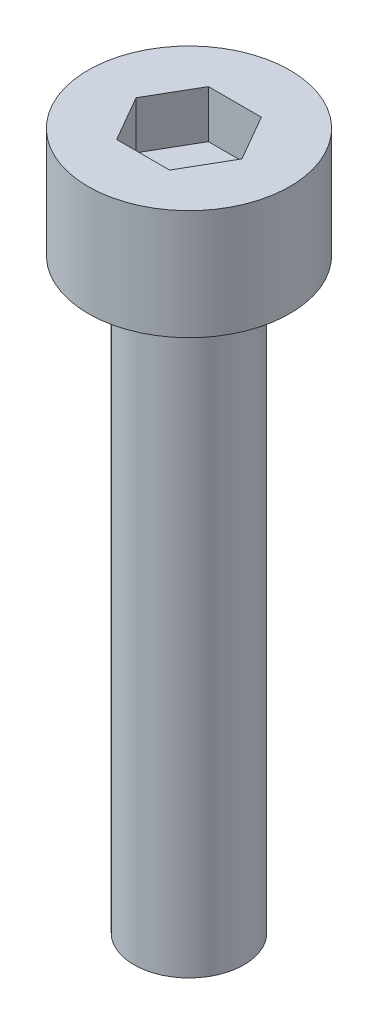
SolidWorks part; units mm, degrees
material "AISI 304"
ref_plane "前视基准面" through (0, 0, 0) normal (0, 0, 1) x (1, 0, 0)
ref_plane "上视基准面" through (0, 0, 0) normal (0, 1, 0) x (1, 0, 0)
ref_plane "右视基准面" through (0, 0, 0) normal (1, 0, 0) x (0, 0, -1)
sketch "草图1" plane through (0, 0, 0) normal (0, 1, 0) x (1, 0, 0)
  circle A0 centre (0, 0) radius 2.75
  dimension "D1" = 5.5
extrude "杯头" add sketch "草图1" along normal blind 3
sketch "草图2" plane through (0, 3, 0) normal (0, 1, 0) x (1, 0, 0)
  line L1 (1.4434, 0) -> (0.7217, 1.25)
  line L2 (0.7217, 1.25) -> (-0.7217, 1.25)
  line L3 (-0.7217, 1.25) -> (-1.4434, 0)
  line L4 (-1.4434, 0) -> (-0.7217, -1.25)
  line L5 (-0.7217, -1.25) -> (0.7217, -1.25)
  line L6 (0.7217, -1.25) -> (1.4434, 0)
  circle A0 centre (0, 0) radius 1.25 construction
  dimension "D1" = 2.5
extrude "内六角口" cut sketch "草图2" against normal blind 1.3
sketch "草图3" plane through (0, 0, 0) normal (0, -1, 0) x (1, 0, 0)
  circle A0 centre (0, 0) radius 1.5
  dimension "D1" = 3
extrude "螺纹长" add sketch "草图3" along normal blind 16
